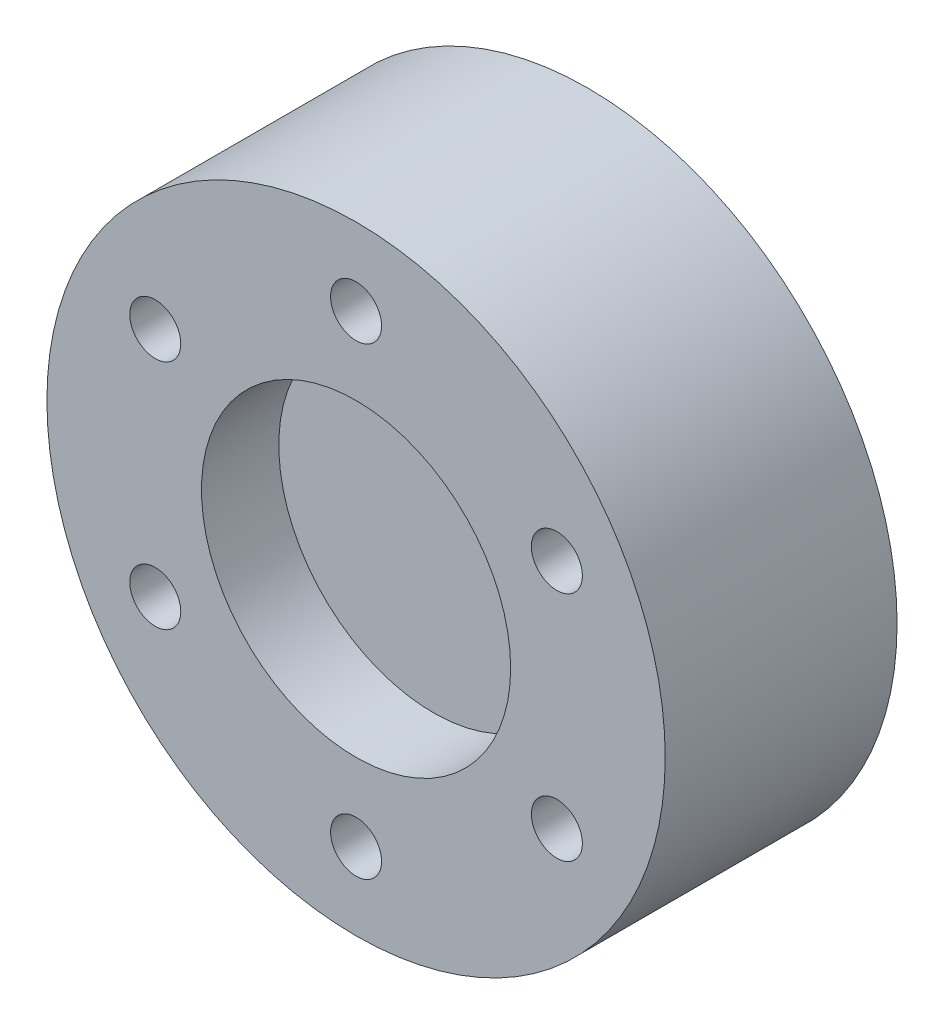
SolidWorks part; units mm, degrees
ref_plane "Front Plane" through (0, 0, 0) normal (0, 0, 1) x (1, 0, 0)
ref_plane "Top Plane" through (0, 0, 0) normal (0, 1, 0) x (1, 0, 0)
ref_plane "Right Plane" through (0, 0, 0) normal (1, 0, 0) x (0, 0, -1)
sketch "Sketch1" plane through (0, 0, 0) normal (0, 0, 1) x (1, 0, 0)
  circle A0 centre (0, 0) radius 20
  dimension "D1" = 40
extrude "Boss-Extrude1" add sketch "Sketch1" along normal blind 15
sketch "Sketch2" plane through (0, 0, 15) normal (0, 0, 1) x (1, 0, 0)
  circle A0 centre (0, 0) radius 10
  dimension "D1" = 20
extrude "Cut-Extrude1" cut sketch "Sketch2" against normal blind 5
hole_wizard "M4x0.7 Tapped Hole1" positions "Sketch3" profile "Sketch4" tap size "M4x0.7" standard "ANSI Metric"
sketch "Sketch3" plane through (0, 0, 15) normal (0, 0, 1) x (1, 0, 0)
  point P0 (0, 15)
  dimension "D1" = 15
sketch "Sketch4" plane through (0, 15, 15) normal (1, 0, 0) x (0, -1, 0)
  line L0 (0, 0) -> (0, 11.0914)
  line L1 (0, 11.0914) -> (1.65, 10.1)
  line L2 (1.65, 10.1) -> (1.65, 0)
  line L5 (1.65, 0) -> (0, 0)
  line L10 (0, 11.0914) -> (-1.65, 10.1) construction
  line L11 (0, -6.35) -> (0, 107.95) construction
  dimension "Tap Drill Dia." = 3.3
  dimension "Tap Drill Depth" = 10.1
  dimension "Drill Angle" = 118
cosmetic thread "Hole Thread1" parameters "D1"=8, "D2"=4
pattern_circular "CirPattern1" count 6 over 360 about axis through (0, 0, 0) along (0, 0, 1) of "M4x0.7 Tapped Hole1"
cosmetic thread "Hole Thread2" parameters "D1"=8, "D2"=4
cosmetic thread "Hole Thread3" parameters "D1"=8, "D2"=4
cosmetic thread "Hole Thread4" parameters "D1"=8, "D2"=4
cosmetic thread "Hole Thread5" parameters "D1"=8, "D2"=4
cosmetic thread "Hole Thread6" parameters "D1"=8, "D2"=4
sketch "Sketch5" plane through (0, 0, 0) normal (0, 0, -1) x (-1, 0, 0)
  circle A0 centre (0, 0) radius 17.5
  dimension "D1" = 35
extrude "Cut-Extrude3" cut sketch "Sketch5" against normal blind 3
